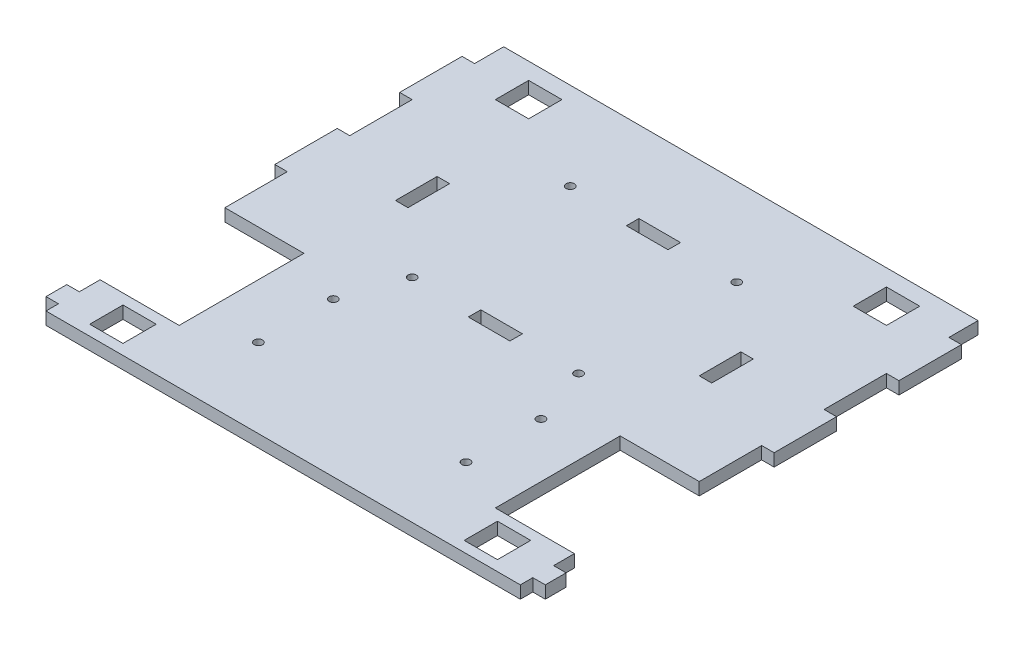
SolidWorks part; units mm, degrees
ref_plane "Alzado" through (0, 0, 0) normal (0, 0, 1) x (1, 0, 0)
ref_plane "Planta" through (0, 0, 0) normal (0, 1, 0) x (1, 0, 0)
ref_plane "Vista lateral" through (0, 0, 0) normal (1, 0, 0) x (0, 0, -1)
sketch "Croquis1" plane through (0, 0, 0) normal (0, 1, 0) x (1, 0, 0)
  line L0 (-57, -15) -> (-38, -15)
  line L1 (57, 60) -> (-57, 60)
  line L2 (57, 60) -> (57, 45)
  line L3 (57, -60) -> (-57, -60)
  line L4 (-57, 60) -> (-57, 45)
  line L5 (57, 60) -> (-57, -60) construction
  line L6 (57, -60) -> (-57, 60) construction
  line L7 (-38, -15) -> (-38, -45)
  line L8 (-38, -45) -> (-57, -45)
  line L9 (0, 60) -> (0, -60) construction
  line L10 (-57, -45) -> (-57, -50)
  line L11 (38, -45) -> (57, -45)
  line L12 (38, -15) -> (38, -45)
  line L13 (57, -15) -> (38, -15)
  line L14 (57, -45) -> (57, -50)
  line L15 (-24.95, -21) -> (-24.95, -39) construction
  line L16 (-5, 29.5) -> (-5, 32.5)
  line L18 (-38, -30) -> (-8.5588, -30) construction
  line L19 (35, 17) -> (35, 7)
  line L20 (5.225, -5.5) -> (-5.225, -5.5)
  line L21 (-35, 17) -> (-35, 7)
  line L22 (-5, 31) -> (-26.2447, 31) construction
  line L23 (47, 40) -> (39, 40)
  line L24 (-5, 32.5) -> (5, 32.5)
  line L25 (5, 32.5) -> (5, 29.5)
  line L26 (35, 17) -> (38, 17)
  line L27 (38, 17) -> (38, 7)
  line L28 (38, 7) -> (35, 7)
  line L29 (-5, -5.5) -> (-5, -8.5)
  line L30 (-5, -8.5) -> (5, -8.5)
  line L31 (5, -8.5) -> (5, -5.5)
  line L32 (-35, 17) -> (-38, 17)
  line L33 (-38, 17) -> (-38, 7)
  line L34 (-38, 7) -> (-35, 7)
  line L35 (0, 12) -> (70.5477, 12) construction
  line L36 (5, 29.5) -> (-5, 29.5)
  line L41 (39, 48) -> (39, 40)
  line L42 (47, 48) -> (39, 48)
  line L43 (-47, 48) -> (-39, 48)
  line L44 (-47, 48) -> (-47, 40)
  line L45 (-47, 40) -> (-39, 40)
  line L46 (-39, 48) -> (-39, 40)
  line L47 (-47, 48) -> (-39, 40) construction
  line L48 (-47, 40) -> (-39, 48) construction
  line L49 (47, 48) -> (47, 40)
  line L50 (49, -55.5) -> (41, -55.5)
  line L51 (41, -47.5) -> (41, -55.5)
  line L52 (49, -47.5) -> (41, -47.5)
  line L53 (49, -47.5) -> (49, -55.5)
  line L55 (-49, -47.5) -> (-49, -55.5)
  line L56 (-49, -47.5) -> (-41, -47.5)
  line L57 (-41, -47.5) -> (-41, -55.5)
  line L58 (-49, -55.5) -> (-41, -55.5)
  line L59 (57, 45) -> (60, 45)
  line L60 (60, 45) -> (60, 30)
  line L61 (60, 30) -> (57, 30)
  line L62 (57, 15) -> (60, 15)
  line L63 (60, 15) -> (60, 0)
  line L64 (60, 0) -> (57, 0)
  line L65 (57, 30) -> (57, 15)
  line L66 (57, 0) -> (57, -15)
  line L67 (-60, 0) -> (-57, 0)
  line L68 (-60, 15) -> (-60, 0)
  line L69 (-57, 15) -> (-60, 15)
  line L70 (-60, 30) -> (-57, 30)
  line L71 (-60, 45) -> (-60, 30)
  line L72 (-57, 45) -> (-60, 45)
  line L73 (-57, 30) -> (-57, 15)
  line L74 (-57, 0) -> (-57, -15)
  line L75 (57, -50) -> (60, -50)
  line L76 (60, -50) -> (60, -55)
  line L77 (60, -55) -> (57, -55)
  line L78 (57, -55) -> (57, -60)
  line L79 (-60, -55) -> (-57, -55)
  line L80 (-60, -50) -> (-60, -55)
  line L81 (-57, -50) -> (-60, -50)
  line L82 (-57, -55) -> (-57, -60)
  circle A0 centre (-20, 31) radius 1
  circle A3 centre (-24.95, -21) radius 1
  circle A4 centre (-24.95, -39) radius 1
  circle A5 centre (24.95, -39) radius 1
  circle A6 centre (24.95, -21) radius 1
  circle A7 centre (20, 31) radius 1
  circle A8 centre (20, -7) radius 1
  circle A9 centre (-20, -7) radius 1
  point P0 (0, 0)
  point P16 (0, 12)
  point P62 (-43, 44)
  dimension "D7" = 18
  dimension "D9" = 2
  dimension "D10" = 35
  dimension "D11" = 2
  dimension "D1" = 114
  dimension "D2" = 120
  dimension "D3" = 19
  dimension "D4" = 30
  dimension "D5" = 15
  dimension "D6" = 13.05
  dimension "D8" = 6
  dimension "D12" = 72
  dimension "D13" = 3
  dimension "D14" = 3
  dimension "D15" = 3
  dimension "D16" = 3
  dimension "D17" = 10
  dimension "D18" = 10
  dimension "D19" = 10
  dimension "D20" = 10
  dimension "D21" = 70
  dimension "D22" = 15
  dimension "D23" = 8
  dimension "D24" = 8
  dimension "D25" = 16
  dimension "D26" = 10
  dimension "D27" = 8
  dimension "D28" = 8
  dimension "D29" = 8
  dimension "D30" = 3
  dimension "D31" = 15
  dimension "D32" = 15
  dimension "D33" = 15
  dimension "D34" = 15
  dimension "D35" = 3
  dimension "D36" = 5
  dimension "D37" = 2.5
  dimension "D38" = 5
  dimension "D39" = 5
  dimension "D40" = 3
  dimension "D41" = 5
extrude "Saliente-Extruir1" add sketch "Croquis1" along normal blind 3
sketch "Croquis2" plane through (0, 3, 0) normal (0, 1, 0) x (1, 0, 0)
  line L0 (-57, 60) -> (-57, 45) construction
  line L1 (-57, 52) -> (57, 52)
  line L2 (-57, 52) -> (-57, 60)
  line L3 (-57, 60) -> (57, 60)
  line L4 (57, 52) -> (57, 60)
  line L5 (-57, 52) -> (57, 60) construction
  line L6 (-57, 60) -> (57, 52) construction
  point P0 (0, 56)
  dimension "D1" = 8
extrude "Cortar-Extruir1" cut sketch "Croquis2" against normal through all
sketch "Croquis3" plane through (0, 3, 0) normal (0, 1, 0) x (1, 0, 0)
  line L1 (57, -58) -> (-57, -58)
  line L2 (57, -58) -> (57, -60)
  line L3 (57, -60) -> (-57, -60)
  line L4 (-57, -58) -> (-57, -60)
  line L5 (57, -58) -> (-57, -60) construction
  line L6 (57, -60) -> (-57, -58) construction
  point P0 (0, -59)
  dimension "D1" = 2
extrude "Cortar-Extruir2" cut sketch "Croquis3" against normal through all
